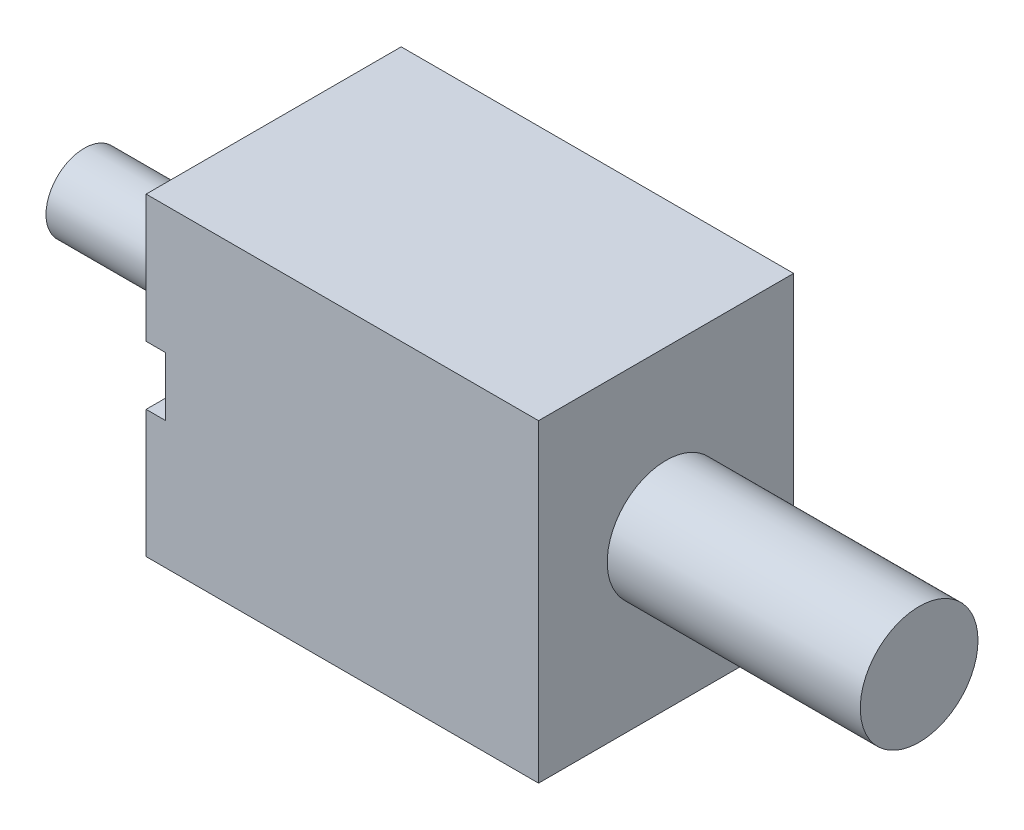
SolidWorks part; units mm, degrees
ref_plane "Front Plane" through (0, 0, 0) normal (0, 0, 1) x (1, 0, 0)
ref_plane "Top Plane" through (0, 0, 0) normal (0, 1, 0) x (1, 0, 0)
ref_plane "Right Plane" through (0, 0, 0) normal (1, 0, 0) x (0, 0, -1)
sketch "Sketch1" plane through (0, 0, 0) normal (0, 1, 0) x (1, 0, 0)
  line L1 (-10, -6.5) -> (10, -6.5)
  line L2 (-10, -6.5) -> (-10, 6.5)
  line L3 (-10, 6.5) -> (10, 6.5)
  line L4 (10, -6.5) -> (10, 6.5)
  line L5 (-10, -6.5) -> (10, 6.5) construction
  line L6 (-10, 6.5) -> (10, -6.5) construction
  point P0 (0, 0)
  dimension "D1" = 13
  dimension "D2" = 20
extrude "Boss-Extrude1" add sketch "Sketch1" along normal blind 16
sketch "Sketch2" plane through (-10, 0, 0) normal (-1, 0, 0) x (0, 0, 1)
  line L0 (0, 16) -> (0, 0) construction
  line L1 (-6.5, 16) -> (6.5, 16) construction
  line L2 (-6.5, 0) -> (6.5, 0) construction
  line L3 (-6.5, 8) -> (6.5, 8) construction
  line L4 (-6.5, 16) -> (-6.5, 0) construction
  line L5 (6.5, 16) -> (6.5, 0) construction
  circle A0 centre (0, 8) radius 1.95
  point P12 (0, 8)
  dimension "D1" = 3.9
extrude "Boss-Extrude2" add sketch "Sketch2" along normal blind 9.6525
sketch "Sketch3" plane through (10, 0, 0) normal (1, 0, 0) x (0, 0, -1)
  line L0 (0, 16) -> (0, 0) construction
  line L1 (-6.5, 16) -> (6.5, 16) construction
  line L2 (-6.5, 8) -> (6.5, 8) construction
  line L3 (-6.5, 16) -> (-6.5, 0) construction
  line L4 (6.5, 16) -> (6.5, 0) construction
  circle A0 centre (0, 8) radius 3
  point P11 (0, 8)
  dimension "D1" = 6
extrude "Boss-Extrude3" add sketch "Sketch3" along normal blind 12.8958
sketch "Sketch4" plane through (0, 0, 6.5) normal (0, 0, 1) x (1, 0, 0)
  line L0 (-10, 8) -> (10, 8) construction
  line L1 (-10, 9.95) -> (-10, 6.05) construction
  line L2 (10, 16) -> (10, 0) construction
  line L3 (-10, 16) -> (-10, 0) construction
  line L4 (-10, 9.5) -> (-9, 9.5)
  line L5 (-10, 9.5) -> (-10, 6.5)
  line L6 (-10, 6.5) -> (-9, 6.5)
  line L7 (-9, 9.5) -> (-9, 6.5)
  dimension "D1" = 3
  dimension "D2" = 1
extrude "Cut-Extrude1" cut sketch "Sketch4" against normal blind 1
